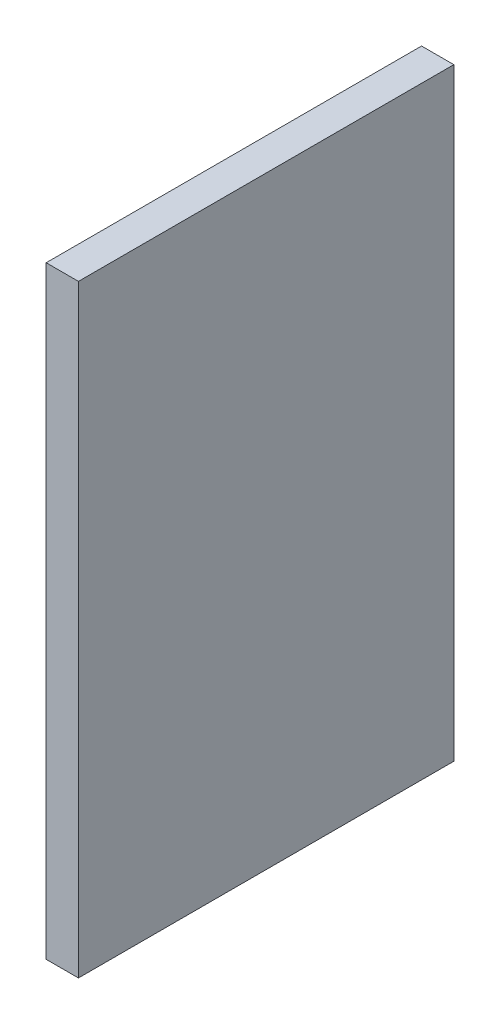
SolidWorks part; units mm, degrees
ref_plane "Спереди" through (0, 0, 0) normal (0, 0, 1) x (1, 0, 0)
ref_plane "Сверху" through (0, 0, 0) normal (0, 1, 0) x (1, 0, 0)
ref_plane "Справа" through (0, 0, 0) normal (1, 0, 0) x (0, 0, -1)
sketch "Эскиз1" plane through (0, 0, 0) normal (1, 0, 0) x (0, 0, -1)
  line L0 (0, 0) -> (28, 0)
  line L1 (28, 0) -> (28, 45)
  line L2 (28, 45) -> (0, 45)
  line L3 (0, 45) -> (0, 0)
extrude "Вытянуть1" add sketch "Эскиз1" along normal blind 2.408
